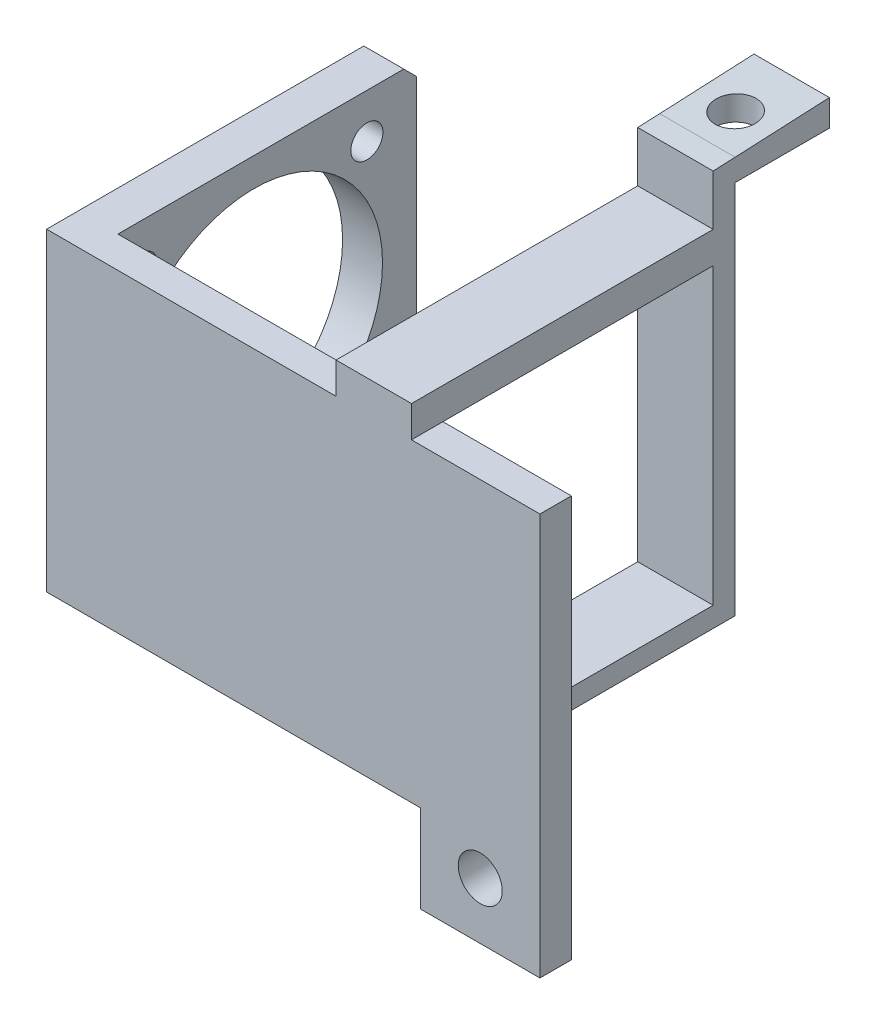
SolidWorks part; units mm, degrees
material "PETG"
ref_plane "Front Plane" through (0, 0, 0) normal (0, 0, 1) x (1, 0, 0)
ref_plane "Top Plane" through (0, 0, 0) normal (0, 1, 0) x (1, 0, 0)
ref_plane "Right Plane" through (0, 0, 0) normal (1, 0, 0) x (0, 0, -1)
sketch "Sketch1" plane through (0, 0, 0) normal (0, 0, 1) x (1, 0, 0)
  line L0 (0, 0) -> (0, 50)
  line L2 (59.5, 50) -> (59.5, 64.061)
  line L3 (59.5, 64.061) -> (78.5, 64.061)
  line L4 (78.5, 64.061) -> (78.5, -13.939)
  line L5 (78.5, -13.939) -> (59.5, -13.939)
  line L6 (59.5, -13.939) -> (59.5, 0)
  line L7 (59.5, 0) -> (0, 0)
  line L8 (58.06, 50) -> (58.06, 55)
  line L9 (58.06, 55) -> (46.06, 55)
  line L10 (46.06, 55) -> (46.06, 50)
  line L11 (0, 50) -> (46.06, 50)
  line L12 (58.06, 50) -> (59.5, 50)
  dimension "D1" = 78
  dimension "D2" = 19
  dimension "D3" = 59.5
  dimension "D4" = 13.939
  dimension "D5" = 14.061
  dimension "D6" = 5
  dimension "D7" = 12
  dimension "D8" = 1.44
extrude "Boss-Extrude1" add sketch "Sketch1" along normal blind 5
sketch "Sketch2" plane through (0, 0, 0) normal (0, 0, -1) x (-1, 0, 0)
  line L1 (0, 0) -> (-6.35, 0)
  line L2 (0, 0) -> (0, 50)
  line L3 (0, 50) -> (-6.35, 50)
  line L4 (-6.35, 0) -> (-6.35, 50)
extrude "Boss-Extrude2" add sketch "Sketch2" along normal blind 52.48
sketch "Sketch3" plane through (6.35, 0, 0) normal (1, 0, 0) x (0, 0, -1)
  line L0 (52.48, 0) -> (0, 0) construction
  line L1 (0, 50) -> (0, 0) construction
  line L2 (52.48, 50) -> (52.48, 0) construction
  line L3 (52.48, 50) -> (0, 50) construction
  line L5 (52.48, 50) -> (47.48, 50)
  line L6 (52.48, 50) -> (52.48, 0)
  line L7 (52.48, 0) -> (47.48, 0)
  line L8 (47.48, 50) -> (47.48, 0)
  circle A0 centre (21.66, 25) radius 20.44
  circle A1 centre (3.695, 42.955) radius 2.555
  circle A2 centre (39.615, 7.045) radius 2.555
  dimension "D1" = 25
  dimension "D2" = 21.66
  dimension "D3" = 12.865
  dimension "D4" = 7.045
  dimension "D5" = 3.695
  dimension "D6" = 7.045
extrude "Cut-Extrude1" cut sketch "Sketch3" against normal up to next
sketch "Sketch4" plane through (0, 0, 0) normal (0, 0, -1) x (-1, 0, 0)
  line L0 (-59.5, -13.939) -> (-78.5, -13.939) construction
  line L1 (-78.5, -13.939) -> (-78.5, 64.061) construction
  line L2 (-78.5, 64.061) -> (-59.5, 64.061) construction
  circle A0 centre (-69, 55.061) radius 3.5
  circle A1 centre (-69, -4.939) radius 3.5
  dimension "D1" = 9
  dimension "D2" = 9.5
  dimension "D3" = 9
extrude "Cut-Extrude2" cut sketch "Sketch4" against normal up to next
sketch "Sketch14" plane through (0, 0, 0) normal (0, 0, -1) x (-1, 0, 0)
  line L0 (-78.5, -13.939) -> (-78.5, 64.061) construction
  line L1 (-59.5, 50) -> (-78.5, 50)
  line L2 (-59.5, 50) -> (-59.5, 65.3162)
  line L3 (-59.5, 65.3162) -> (-78.5, 65.3162)
  line L4 (-78.5, 50) -> (-78.5, 65.3162)
  line L5 (-59.5, 64.061) -> (-59.5, 50) construction
extrude "Cut-Extrude6" cut sketch "Sketch14" against normal up to next
sketch "Sketch15" plane through (0, 0, 0) normal (0, 0, -1) x (-1, 0, 0)
  line L1 (-58.06, 0) -> (-46.06, 0)
  line L2 (-58.06, 0) -> (-58.06, 3.2)
  line L3 (-58.06, 3.2) -> (-46.06, 3.2)
  line L4 (-46.06, 0) -> (-46.06, 3.2)
  line L5 (-6.35, 0) -> (-59.5, 0) construction
  line L6 (-59.5, 0) -> (-59.5, -13.939) construction
  dimension "D1" = 12
  dimension "D2" = 3.2
  dimension "D3" = 1.44
extrude "Boss-Extrude7" add sketch "Sketch15" along normal blind 46.5
sketch "Sketch16" plane through (0, 3.2, 0) normal (0, 1, 0) x (1, 0, 0)
  line L0 (58.06, 46.5) -> (58.06, 0) construction
  line L1 (46.06, 46.5) -> (58.06, 46.5)
  line L2 (46.06, 46.5) -> (46.06, 43)
  line L3 (46.06, 43) -> (58.06, 43)
  line L4 (58.06, 46.5) -> (58.06, 43)
extrude "Boss-Extrude8" add sketch "Sketch16" along normal up to surface (59.9966 mm away)
sketch "Sketch17" plane through (0, 0, -46.5) normal (0, 0, -1) x (-1, 0, 0)
  line L0 (-46.06, 0) -> (-46.06, 63.1966) construction
  line L1 (-58.06, 63.1966) -> (-46.06, 63.1966)
  line L2 (-58.06, 63.1966) -> (-58.06, 59.6966)
  line L3 (-58.06, 59.6966) -> (-46.06, 59.6966)
  line L4 (-46.06, 63.1966) -> (-46.06, 59.6966)
extrude "Boss-Extrude9" add sketch "Sketch17" along normal blind 15
chamfer "Chamfer2" distance 2 angle 45 2 edges at (3.175, 0, -47.48) (3.175, 50, -47.48)
sketch "Sketch10" plane through (0, 0, 0) normal (0, 0, -1) x (-1, 0, 0)
  line L0 (-59.5, 0) -> (-59.5, 5.9818)
  line L1 (-59.5, 5.9818) -> (-36.653, 5.9818)
  line L2 (-36.653, 5.9818) -> (-36.653, 0)
  line L3 (-6.35, 0) -> (-46.06, 0) construction
  line L4 (-36.653, 0) -> (-59.5, 0)
sketch "Sketch22" plane through (0, 63.1966, 0) normal (0, 1, 0) x (1, 0, 0)
  line L1 (46.06, 61.5) -> (58.06, 61.5)
  line L2 (46.06, 61.5) -> (46.06, 46.5)
  line L3 (46.06, 46.5) -> (58.06, 46.5)
  line L4 (58.06, 61.5) -> (58.06, 46.5)
extrude "Boss-Extrude10" add sketch "Sketch22" along normal blind 0.72
sketch "Sketch23" plane through (58.06, 0, 0) normal (1, 0, 0) x (0, 0, -1)
  line L0 (46.5, 63.9166) -> (46.5, 63.1966)
  line L1 (46.5, 63.1966) -> (61.5, 63.9166)
  line L2 (61.5, 63.9166) -> (46.5, 63.9166)
extrude "Cut-Extrude8" cut sketch "Sketch23" against normal up to next
sketch "Sketch18" plane through (0, 59.6966, 0) normal (0, -1, 0) x (1, 0, 0)
  line L0 (58.06, -46.5) -> (46.06, -46.5) construction
  line L2 (46.06, -52.57) -> (58.06, -52.57) construction
  line L4 (58.06, -61.5) -> (58.06, -46.5) construction
  line L5 (46.06, -61.5) -> (46.06, -46.5) construction
  circle A0 centre (52.06, -52.57) radius 3.25
  point P7 (52.06, -52.57)
  dimension "D1" = 6.07
  dimension "D2" = 6.5
extrude "Cut-Extrude7" cut sketch "Sketch18" against normal up to next
pattern_circular "CirPattern2" count 2 over 90 about axis through (0, 25, -21.66) along (1, 0, 0) of "Cut-Extrude1"
sketch "Sketch24" plane through (0, 0, 0) normal (0, 0, -1) x (-1, 0, 0)
  line L1 (-58.06, 55) -> (-46.06, 55)
  line L2 (-58.06, 55) -> (-58.06, 50)
  line L3 (-58.06, 50) -> (-46.06, 50)
  line L4 (-46.06, 55) -> (-46.06, 50)
extrude "Boss-Extrude11" add sketch "Sketch24" along normal up to body separate body
